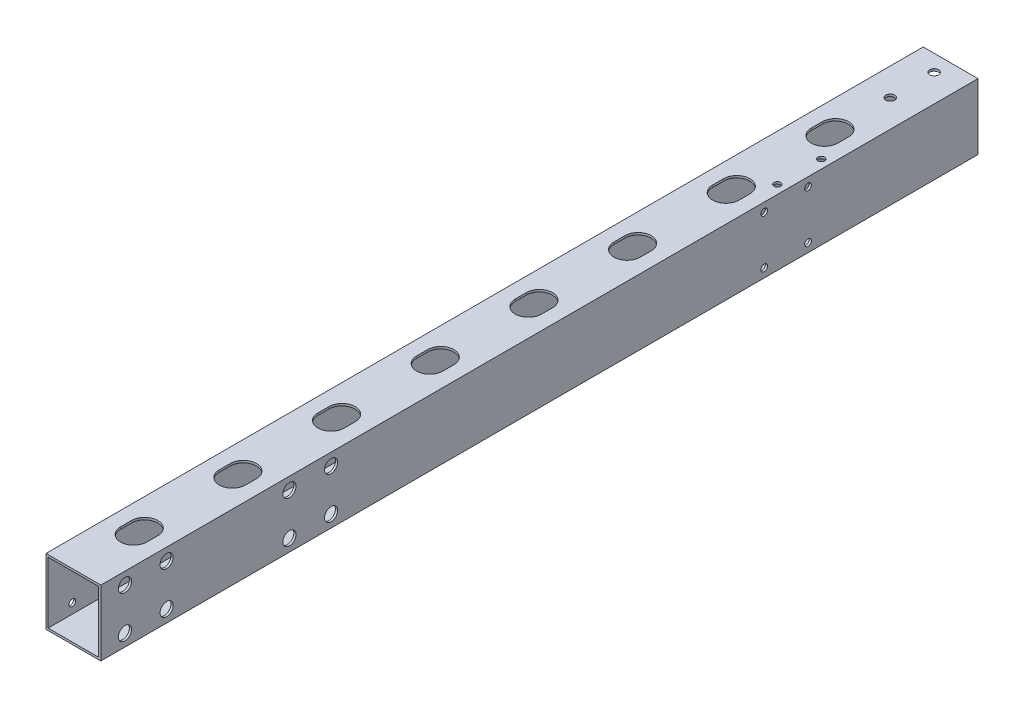
SolidWorks part; units mm, degrees
material "6063-T5"
ref_plane "前视基准面" through (0, 0, 0) normal (0, 0, 1) x (1, 0, 0)
ref_plane "上视基准面" through (0, 0, 0) normal (0, 1, 0) x (1, 0, 0)
ref_plane "右视基准面" through (0, 0, 0) normal (1, 0, 0) x (0, 0, -1)
other "Configuration Table"
sketch "草图1" plane through (0, 0, 0) normal (0, 0, 1) x (1, 0, 0)
  line L1 (-12.5, -15) -> (12.5, -15)
  line L2 (-12.5, -15) -> (-12.5, 15)
  line L3 (-12.5, 15) -> (12.5, 15)
  line L4 (12.5, -15) -> (12.5, 15)
  line L5 (-12.5, -15) -> (12.5, 15) construction
  line L6 (-12.5, 15) -> (12.5, -15) construction
  point P0 (0, 0)
  dimension "D1" = 30
  dimension "D2" = 25
extrude "凸台-拉伸1" add sketch "草图1" along normal mid plane 400
sketch "草图2" plane through (0, 0, 0) normal (0, 0, 1) x (1, 0, 0)
  line L0 (11.5, 14) -> (-11.5, 14)
  line L1 (-11.5, 14) -> (-11.5, -14)
  line L2 (-11.5, -14) -> (11.5, -14)
  line L3 (11.5, -14) -> (11.5, 14)
  line L4 (12.5, -15) -> (12.5, 15)
  line L5 (12.5, 15) -> (-12.5, 15)
  line L6 (-12.5, 15) -> (-12.5, -15)
  line L7 (-12.5, -15) -> (12.5, -15)
  line L8 (12.5, -15) -> (12.5, 15)
  line L9 (12.5, 15) -> (-12.5, 15)
  line L10 (-12.5, 15) -> (-12.5, -15)
  line L11 (-12.5, -15) -> (12.5, -15)
  dimension "D1" = 0
  dimension "D2" = 1
extrude "切除-拉伸1" cut sketch "草图2" against normal mid plane 400 flip side to cut
sketch "草图3" plane through (0, 15, 0) normal (0, 1, 0) x (1, 0, 0)
  circle A5 centre (0, 172.5) radius 2.025
  circle A6 centre (0, 192.5) radius 2.025
  dimension "D1" = 4.05
extrude "切除-拉伸2" cut sketch "草图3" against normal through all
sketch "草图4" plane through (12.5, 0, 0) normal (1, 0, 0) x (0, 0, -1)
  circle A0 centre (-170, -9.5) radius 1.525
  circle A1 centre (-189, -9.5) radius 1.525
  circle A2 centre (-189, 9.5) radius 1.525
  circle A3 centre (-170, 9.5) radius 1.525
  circle A4 centre (-170, 9.5) radius 1.2 construction
  circle A5 centre (-170, -9.5) radius 1.5 construction
  circle A6 centre (-189, 9.5) radius 1.2 construction
  circle A7 centre (-189, -9.5) radius 1.2 construction
  dimension "D1" = 3.05
extrude "切除-拉伸3" cut sketch "草图4" against normal through all both
sketch "草图5" plane through (12.5, 0, 0) normal (1, 0, 0) x (0, 0, -1)
  circle A0 centre (-95, 9.5) radius 1.525
  circle A1 centre (-114, 9.5) radius 1.525
  circle A2 centre (-114, -9.5) radius 1.525
  circle A3 centre (-95, -9.5) radius 1.525
  circle A4 centre (-114, 9.5) radius 1.2 construction
  circle A5 centre (-95, 9.5) radius 1.5 construction
  circle A6 centre (-114, -9.5) radius 1.5 construction
  circle A7 centre (-95, -9.5) radius 1.5 construction
  dimension "D1" = 3.05
extrude "切除-拉伸4" cut sketch "草图5" against normal through all both
sketch "草图6" plane through (12.5, 0, 0) normal (1, 0, 0) x (0, 0, -1)
  circle A0 centre (-170, 9.5) radius 3
  circle A1 centre (-170, -9.5) radius 3
  circle A2 centre (-189, -9.5) radius 3
  circle A3 centre (-189, 9.5) radius 3
  dimension "D1" = 6
extrude "切除-拉伸5" cut sketch "草图6" against normal blind 5
sketch "草图7" plane through (12.5, 0, 0) normal (1, 0, 0) x (0, 0, -1)
  circle A0 centre (-114, 9.5) radius 3
  circle A1 centre (-95, 9.5) radius 3
  circle A2 centre (-95, -9.5) radius 3
  circle A3 centre (-114, -9.5) radius 3
  dimension "D1" = 6
extrude "切除-拉伸6" cut sketch "草图7" against normal blind 5
sketch "草图8" plane through (0, 15, 0) normal (0, 1, 0) x (1, 0, 0)
  line L0 (0, -172.5) -> (0, -167.5) construction
  line L1 (-6, -172.5) -> (-6, -167.5)
  line L2 (6, -172.5) -> (6, -167.5)
  line L3 (12.5, -200) -> (-12.5, -200) construction
  arc A0 (-6, -172.5) -> (6, -172.5) centre (0, -172.5) ccw
  arc A1 (6, -167.5) -> (-6, -167.5) centre (0, -167.5) ccw
  point P3 (0, -170)
  dimension "D2" = 6
  dimension "D1" = 5
  dimension "D3" = 30
extrude "切除-拉伸7" cut sketch "草图8" against normal through all both and the other way through all
pattern_linear "阵列(线性)1" count 8 spacing 45 along (0, 0, -1) of "切除-拉伸7"
sketch "草图9" plane through (12.5, 0, 0) normal (1, 0, 0) x (0, 0, -1)
  line L0 (122.5, -15) -> (122.5, 15) construction
  line L1 (-200, -15) -> (200, -15) construction
  line L2 (-200, 15) -> (200, 15) construction
  line L3 (200, -15) -> (200, 15) construction
  line L4 (200, 0) -> (122.5, 0) construction
  circle A0 centre (112.5, 10.5) radius 1.525
  circle A1 centre (132.5, 10.5) radius 1.525
  circle A2 centre (132.5, -10.5) radius 1.525
  circle A3 centre (112.5, -10.5) radius 1.525
  dimension "D2" = 3.05
  dimension "D3" = 4.5
  dimension "D4" = 20
  dimension "D5" = 10
  dimension "D1" = 77.5
sketch "草图10" plane through (0, 15, 0) normal (0, 1, 0) x (1, 0, 0)
  line L0 (0, 136.5) -> (0, 108.5) construction
  line L1 (0, 122.5) -> (12.5, 122.5) construction
  line L2 (12.5, -200) -> (12.5, 200) construction
  circle A0 centre (8.5, 112.5) radius 1.525
  circle A1 centre (8.5, 132.5) radius 1.525
  arc A4 (-6, 142.5) -> (6, 142.5) centre (0, 142.5) ccw construction
  arc A5 (6, 102.5) -> (-6, 102.5) centre (0, 102.5) ccw construction
  dimension "D1" = 3.05
  dimension "D2" = 20
  dimension "D3" = 4
extrude "切除-拉伸9" cut sketch "草图10" against normal through all
sketch "草图11" plane through (12.5, 0, 0) normal (1, 0, 0) x (0, 0, -1)
  line L0 (-200, -15) -> (200, -15) construction
  line L1 (200, -15) -> (200, 15) construction
  line L2 (-200, 15) -> (200, 15) construction
  circle A0 centre (122.5, 11) radius 1.525
  circle A1 centre (102.5, 11) radius 1.525
  circle A2 centre (102.5, -11) radius 1.525
  circle A3 centre (122.5, -11) radius 1.525
  dimension "D1" = 3.05
  dimension "D2" = 3.05
  dimension "D4" = 77.5
  dimension "D5" = 20
  dimension "D6" = 4
  dimension "D7" = 4
  dimension "D8" = 20
  dimension "D3" = 4
extrude "切除-拉伸10" cut sketch "草图11" against normal blind 3
